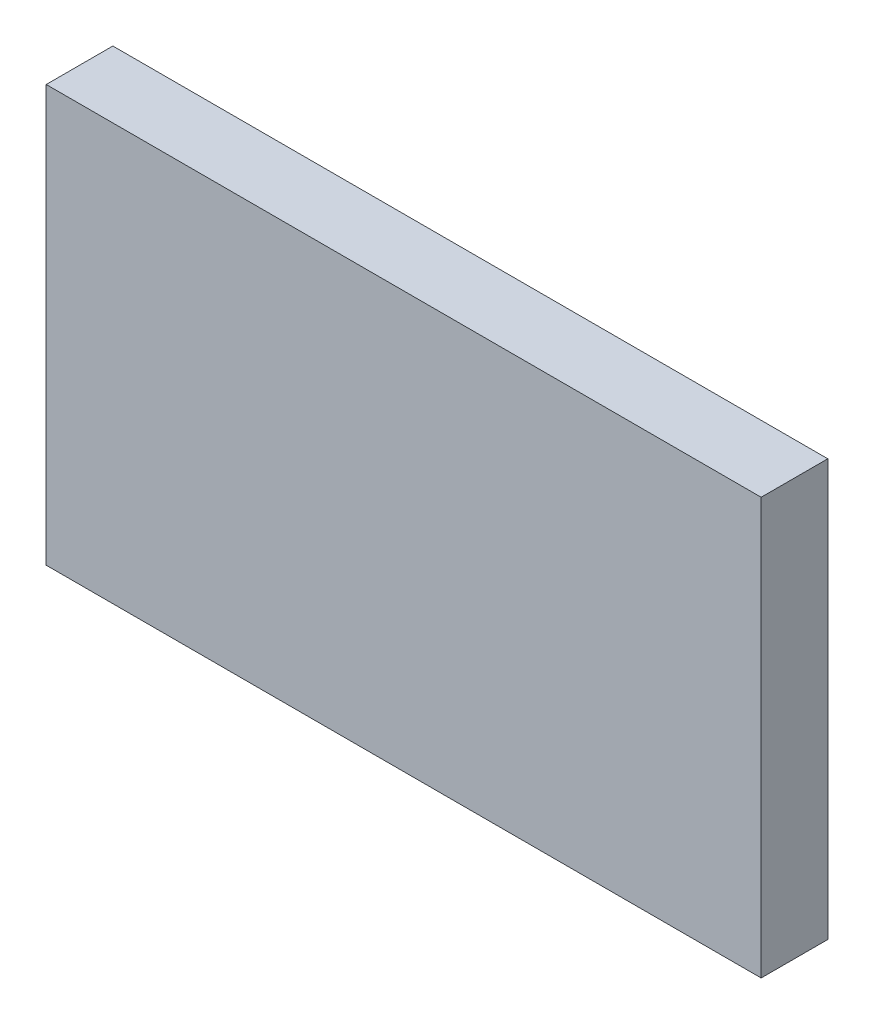
SolidWorks part; units mm, degrees
ref_plane "前视基准面" through (0, 0, 0) normal (0, 0, 1) x (1, 0, 0)
ref_plane "上视基准面" through (0, 0, 0) normal (0, 1, 0) x (1, 0, 0)
ref_plane "右视基准面" through (0, 0, 0) normal (1, 0, 0) x (0, 0, -1)
sketch "草图1" plane through (0, 0, 0) normal (0, 0, 1) x (1, 0, 0)
  line L1 (53.6398, 31.2373) -> (-53.6398, 31.2373)
  line L2 (53.6398, 31.2373) -> (53.6398, -31.2373)
  line L3 (53.6398, -31.2373) -> (-53.6398, -31.2373)
  line L4 (-53.6398, 31.2373) -> (-53.6398, -31.2373)
  line L5 (53.6398, 31.2373) -> (-53.6398, -31.2373) construction
  line L6 (53.6398, -31.2373) -> (-53.6398, 31.2373) construction
  point P0 (0, 0)
extrude "凸台-拉伸1" add sketch "草图1" along normal blind 10
